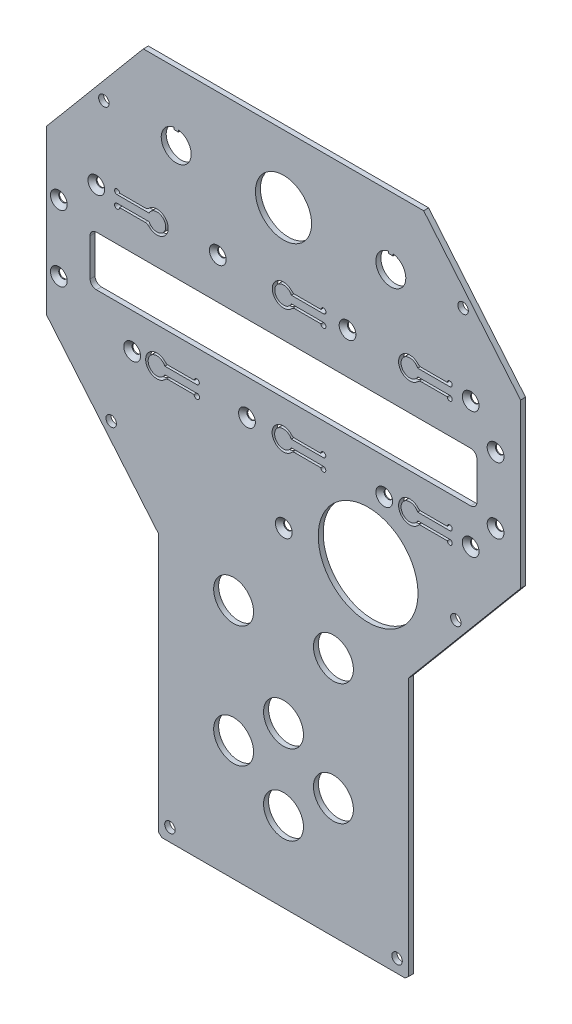
SolidWorks part; units mm, degrees
ref_plane "Plano frontal" through (0, 0, 0) normal (0, 0, 1) x (1, 0, 0)
ref_plane "Plano superior" through (0, 0, 0) normal (0, 1, 0) x (1, 0, 0)
ref_plane "Plano direito" through (0, 0, 0) normal (1, 0, 0) x (0, 0, -1)
sketch "Esboço1" plane through (0, 0, 0) normal (0, 0, 1) x (1, 0, 0)
  line L6 (55.321, 133.8096) -> (-57.007, 133.8096)
  line L7 (-57.007, 133.8096) -> (-95.843, 87.5267)
  line L8 (-95.843, 87.5267) -> (-95.843, 22.1402)
  line L9 (-95.843, 22.1402) -> (-50.843, -31.4887)
  line L10 (-50.843, -31.4887) -> (-50.843, -135.0827)
  line L11 (-50.843, -135.0827) -> (-49.5229, -136.1904)
  line L12 (-49.5229, -136.1904) -> (47.8369, -136.1904)
  line L13 (49.157, -135.0827) -> (47.8369, -136.1904)
  line L14 (49.157, -31.4887) -> (49.157, -135.0827)
  line L15 (94.157, 22.1402) -> (49.157, -31.4887)
  line L16 (94.157, 87.5267) -> (94.157, 22.1402)
  line L17 (55.321, 133.8096) -> (94.157, 87.5267)
  point P1 (0, 0)
  point P2 (0, 0)
  point P16 (-0.843, -136.1904)
  point P17 (-0.843, 133.8096)
  dimension "D2" = 140
extrude "Ressalto-extrusão1" add sketch "Esboço1" along normal blind 2
sketch "Esboço2" plane through (0, 0, 2) normal (0, 0, 1) x (1, 0, 0)
  line L0 (-0.843, -146.6722) -> (-0.843, 180.0647) construction
  line L1 (-95.843, 87.5267) -> (-95.843, 22.1402) construction
  line L2 (55.321, 133.8096) -> (-57.007, 133.8096) construction
  line L3 (-95.843, 22.1402) -> (-50.843, -31.4887) construction
  line L6 (49.157, -135.0827) -> (49.157, -31.4887) construction
  line L7 (-49.5229, -136.1904) -> (47.8369, -136.1904) construction
  line L9 (-50.843, -31.4887) -> (-50.843, -135.0827) construction
  circle A0 centre (-72.8144, 107.9499) radius 2.1
  circle A1 centre (-46.343, -130.9644) radius 2.1
  circle A2 centre (44.657, -130.9644) radius 2.1
  circle A3 centre (71.1284, 107.9499) radius 2.1
  circle A4 centre (-69.8958, -1.7817) radius 2.1
  circle A5 centre (68.2098, -1.7817) radius 2.1
  dimension "D1" = 23.0286
  dimension "D2" = 4.5
  dimension "D3" = 4.5
  dimension "D7" = 25.8597
  dimension "D4" = 5.226
  dimension "D11" = 4.5
extrude "Corte-extrusão1" cut sketch "Esboço2" against normal up to next
sketch "Esboço3" plane through (0, 0, 2) normal (0, 0, 1) x (1, 0, 0)
  line L0 (-95.843, 87.5267) -> (-95.843, 22.1402) construction
  line L1 (-49.5229, -136.1904) -> (47.8369, -136.1904) construction
  line L2 (-75.843, 40.8096) -> (74.157, 40.8096)
  line L3 (-78.343, 43.3096) -> (-78.343, 58.3096)
  line L4 (-75.843, 60.8096) -> (74.157, 60.8096)
  line L5 (76.657, 43.3096) -> (76.657, 58.3096)
  line L6 (-78.343, 40.8096) -> (76.657, 60.8096) construction
  line L7 (-78.343, 60.8096) -> (76.657, 40.8096) construction
  arc A0 (74.157, 60.8096) -> (76.657, 58.3096) centre (74.157, 58.3096) cw
  arc A1 (74.157, 40.8096) -> (76.657, 43.3096) centre (74.157, 43.3096) ccw
  arc A2 (-75.843, 40.8096) -> (-78.343, 43.3096) centre (-75.843, 43.3096) cw
  arc A3 (-78.343, 58.3096) -> (-75.843, 60.8096) centre (-75.843, 58.3096) cw
  dimension "D1" = 2.5
  dimension "D2" = 155
  dimension "D3" = 20
  dimension "D4" = 17.5
  dimension "D5" = 177
extrude "Corte-extrusão2" cut sketch "Esboço3" against normal up to next
sketch "Esboço4" plane through (0, 0, 2) normal (0, 0, 1) x (1, 0, 0)
  line L2 (-49.5229, -136.1904) -> (47.8369, -136.1904) construction
  line L3 (94.157, 22.1402) -> (94.157, 87.5267) construction
  circle A0 centre (33.0563, -0.1904) radius 20
  dimension "D1" = 136
  dimension "D2" = 61.1007
extrude "Corte-extrusão3" cut sketch "Esboço4" against normal up to next
sketch "Esboço5" plane through (0, 0, 2) normal (0, 0, 1) x (1, 0, 0)
  line L1 (-50.843, -31.4887) -> (-50.843, -135.0827) construction
  line L2 (55.321, 133.8096) -> (-57.007, 133.8096) construction
  line L3 (-44.743, 112.7417) -> (-44.743, 111.9417)
  line L4 (-44.743, 111.9417) -> (-42.943, 111.9417)
  line L5 (-42.943, 111.9417) -> (-42.943, 112.7417)
  line L6 (41.257, 112.7417) -> (41.257, 111.9417)
  line L7 (41.257, 111.9417) -> (43.057, 111.9417)
  line L8 (43.057, 111.9417) -> (43.057, 112.7417)
  line L9 (-20.843, -39.5203) -> (19.157, -39.5203) construction
  line L11 (-50.843, -56.8553) -> (49.157, -56.8553) construction
  line L12 (49.157, -135.0827) -> (49.157, -31.4887) construction
  circle A0 centre (-20.843, -88.1059) radius 8
  circle A1 centre (19.157, -88.1059) radius 8
  circle A2 centre (-0.843, -104.1412) radius 8
  circle A3 centre (-0.843, -72.1234) radius 8
  circle A4 centre (-20.843, -39.5203) radius 8
  circle A5 centre (19.157, -39.5203) radius 8
  circle A6 centre (-0.843, 106.8096) radius 11.25
  arc A7 (-44.743, 112.7417) -> (-42.943, 112.7417) centre (-43.843, 106.8096) ccw
  arc A8 (41.257, 112.7417) -> (43.057, 112.7417) centre (42.157, 106.8096) ccw
  point P1 (-0.843, -39.5203)
  point P3 (-20.843, -39.5203)
  point P10 (-0.843, -56.8553)
  dimension "D3" = 40
  dimension "D11" = 27
  dimension "D12" = 43
  dimension "D13" = 43
  dimension "D14" = 22.5
  dimension "D15" = 12
  dimension "D16" = 12
  dimension "D18" = 1.8
  dimension "D19" = 0.9
  dimension "D20" = 0.8
  dimension "D21" = 1.8
  dimension "D22" = 0.9
  dimension "D23" = 0.8
extrude "Corte-extrusão4" cut sketch "Esboço5" against normal up to next
sketch "Esboço10" plane through (0, 0, 2) normal (0, 0, 1) x (1, 0, 0)
  line L3 (94.157, 22.1402) -> (94.157, 87.5267) construction
  line L4 (74.157, 60.8096) -> (-75.843, 60.8096) construction
  circle A0 centre (-61.4827, 26.6206) radius 1.75
  circle A1 centre (-15.4827, 26.6206) radius 1.75
  circle A2 centre (39.5173, 26.6206) radius 1.75
  circle A3 centre (84.131, 37.971) radius 1.6
  circle A4 centre (84.131, 64.471) radius 1.6
  circle A5 centre (-90.869, 64.471) radius 1.6
  circle A6 centre (-90.869, 37.971) radius 1.6
  circle A7 centre (-27.183, 77.1996) radius 1.75
  circle A8 centre (24.817, 77.1996) radius 1.75
  circle A9 centre (-0.7327, -4.3294) radius 2
  dimension "D1" = 69.3401
  dimension "D2" = 16.39
  dimension "D3" = 52
  dimension "D4" = 30.95
  dimension "D5" = 14.75
hole_wizard "Escareado para parafuso Allen sextavado escareado de M32" positions "3DSketch3" profile "Esboço11" countersink size "M3" standard "ISO" end condition through all
sketch3d "3DSketch3"
  point P0 (-90.869, 64.471, 2)
  point P3 (-90.869, 37.971, 2)
  point P6 (-61.4827, 26.6206, 2)
  point P9 (-15.4827, 26.6206, 2)
  point P12 (39.5173, 26.6206, 2)
  point P15 (84.131, 37.971, 2)
  point P18 (84.131, 64.471, 2)
  point P21 (24.817, 77.1996, 2)
  point P24 (-27.183, 77.1996, 2)
  point P32 (-0.7327, -4.3294, 2)
sketch "Esboço11" plane through (-90.869, 64.471, 2) normal (1, 0, 0) x (0, -1, 0)
  line L0 (0, 0) -> (0, 2)
  line L1 (0, 2) -> (1.7, 2)
  line L2 (1.7, 2) -> (1.7, 1.66)
  line L3 (1.7, 1.66) -> (3.36, 0)
  line L5 (3.36, 0) -> (0, 0)
  line L6 (-1.7, 1.66) -> (-3.36, 0) construction
  line L11 (0, -6.35) -> (0, 107.95) construction
  dimension "Thru Hole Dia." = 3.4
  dimension "Thru Hole Depth" = 2
  dimension "Near C'Sink Dia." = 6.72
  dimension "Near C'Sink Angle" = 90
sketch "Esboço12" plane through (0, 0, 2) normal (0, 0, 1) x (1, 0, 0)
  line L0 (-75.843, 40.8096) -> (74.157, 40.8096) construction
  line L1 (74.157, 60.8096) -> (-75.843, 60.8096) construction
  line L2 (94.157, 22.1402) -> (94.157, 87.5267) construction
  line L3 (52.9293, 28.0196) -> (65.767, 28.0196)
  line L5 (64.767, 29.0196) -> (53.5087, 29.0196)
  line L6 (52.9293, 25.0196) -> (65.767, 25.0196)
  line L7 (2.2593, 28.0196) -> (15.097, 28.0196)
  line L8 (64.767, 24.0196) -> (53.5087, 24.0196)
  line L9 (14.097, 24.0196) -> (2.8387, 24.0196)
  line L10 (14.097, 29.0196) -> (2.8387, 29.0196)
  line L11 (2.2593, 25.0196) -> (15.097, 25.0196)
  line L12 (-48.4107, 28.0196) -> (-35.573, 28.0196)
  line L13 (-36.6534, 24.0196) -> (-47.8313, 24.0196)
  line L14 (-36.573, 29.0196) -> (-47.8313, 29.0196)
  line L15 (-48.4107, 25.0196) -> (-35.9821, 25.0196)
  line L25 (2.3293, 77.9796) -> (15.167, 77.9796)
  line L26 (52.9293, 77.9796) -> (65.767, 77.9796)
  line L27 (14.167, 78.9796) -> (2.9087, 78.9796)
  line L28 (2.3293, 74.9796) -> (15.167, 74.9796)
  line L29 (-54.6953, 77.9796) -> (-67.533, 77.9796)
  line L30 (14.167, 73.9796) -> (2.9087, 73.9796)
  line L31 (64.767, 78.9796) -> (53.5087, 78.9796)
  line L32 (52.9293, 74.9796) -> (65.767, 74.9796)
  line L34 (64.767, 73.9796) -> (53.5087, 73.9796)
  line L35 (-66.533, 78.9796) -> (-55.2746, 78.9796)
  line L36 (-54.6953, 74.9796) -> (-67.533, 74.9796)
  line L38 (-66.533, 73.9796) -> (-55.2746, 73.9796)
  arc A0 (53.5087, 29.0196) -> (53.5087, 24.0196) centre (49.767, 26.5196) ccw
  arc A2 (15.097, 25.0196) -> (14.097, 24.0196) centre (15.097, 24.0196) cw
  arc A3 (-47.8313, 29.0196) -> (-47.8313, 24.0196) centre (-51.573, 26.5196) ccw
  arc A4 (-55.2746, 73.9796) -> (-55.2746, 78.9796) centre (-51.533, 76.4796) ccw
  arc A5 (2.9087, 78.9796) -> (2.9087, 73.9796) centre (-0.833, 76.4796) ccw
  arc A6 (53.5087, 78.9796) -> (53.5087, 73.9796) centre (49.767, 76.4796) ccw
  arc A7 (52.9293, 28.0196) -> (52.9293, 25.0196) centre (49.767, 26.5196) ccw
  arc A8 (65.767, 28.0196) -> (64.767, 29.0196) centre (65.767, 29.0196) ccw
  arc A9 (64.767, 24.0196) -> (65.767, 25.0196) centre (65.767, 24.0196) ccw
  arc A10 (15.097, 28.0196) -> (14.097, 29.0196) centre (15.097, 29.0196) ccw
  arc A11 (2.8387, 29.0196) -> (2.8387, 24.0196) centre (-0.903, 26.5196) ccw
  arc A12 (2.2593, 28.0196) -> (2.2593, 25.0196) centre (-0.903, 26.5196) ccw
  arc A13 (-35.573, 28.0196) -> (-36.573, 29.0196) centre (-35.573, 29.0196) ccw
  arc A14 (-35.9821, 25.0196) -> (-36.6534, 24.0196) centre (-35.573, 24.0196) cw
  arc A17 (-48.4107, 28.0196) -> (-48.4107, 25.0196) centre (-51.573, 26.5196) ccw
  arc A22 (15.167, 77.9796) -> (14.167, 78.9796) centre (15.167, 78.9796) ccw
  arc A23 (52.9293, 77.9796) -> (52.9293, 74.9796) centre (49.767, 76.4796) ccw
  arc A24 (2.3293, 77.9796) -> (2.3293, 74.9796) centre (-0.833, 76.4796) ccw
  arc A25 (14.167, 73.9796) -> (15.167, 74.9796) centre (15.167, 73.9796) ccw
  arc A26 (65.767, 77.9796) -> (64.767, 78.9796) centre (65.767, 78.9796) ccw
  arc A27 (64.767, 73.9796) -> (65.767, 74.9796) centre (65.767, 73.9796) ccw
  arc A28 (-54.6953, 74.9796) -> (-54.6953, 77.9796) centre (-51.533, 76.4796) ccw
  arc A29 (-66.533, 78.9796) -> (-67.533, 77.9796) centre (-67.533, 78.9796) ccw
  arc A30 (-67.533, 74.9796) -> (-66.533, 73.9796) centre (-67.533, 73.9796) ccw
  dimension "D2" = 14.29
  dimension "D5" = 15.67
  dimension "D6" = 44.39
  dimension "D7" = 50.6
  dimension "D8" = 50.7
  dimension "D9" = 1
  dimension "D13" = 16
  dimension "D14" = 4.5
  dimension "D15" = 3.5
  dimension "D16" = 3.5
  dimension "D17" = 4.5
  dimension "D10" = 1
  dimension "D18" = 16
  dimension "D22" = 3.5
  dimension "D19" = 44.39
  dimension "D33" = 4.5
  dimension "D38" = 4.5
  dimension "D42" = 1
  dimension "D39" = 3.5
  dimension "D44" = 16
  dimension "D46" = 4.5
  dimension "D47" = 3.5
  dimension "D45" = 16
  dimension "D50" = 4.5
  dimension "D51" = 3.5
  dimension "D52" = 16
  dimension "D21" = 50.67
  dimension "D11" = 3
  dimension "D12" = 1.5
  dimension "D20" = 50.67
  dimension "D23" = 16
  dimension "D40" = 3
  dimension "D41" = 1.5
  dimension "D43" = 1
extrude "Corte-extrusão5" cut sketch "Esboço12" against normal blind 10
fillet "Filete1" radius 2 11 edges at (-47.8313, 24.0196, 1) (2.8387, 24.0196, 1) (53.5087, 73.9796, 1) (-47.8313, 29.0196, 1) (2.8387, 29.0196, 1) (53.5087, 29.0196, 1) (53.5087, 78.9796, 1) (2.9087, 73.9796, 1) (2.9087, 78.9796, 1) (-55.2746, 73.9796, 1) (-55.2746, 78.9796, 1)
sketch "Esboço13" plane through (0, 0, 2) normal (0, 0, 1) x (1, 0, 0)
  line L0 (74.157, 60.8096) -> (-75.843, 60.8096) construction
  line L1 (-95.843, 87.5267) -> (-95.843, 22.1402) construction
  line L2 (94.157, 22.1402) -> (94.157, 87.5267) construction
  circle A0 centre (-75.843, 77.1996) radius 2
  circle A1 centre (74.157, 77.1996) radius 2
  circle A9 centre (74.157, 26.6206) radius 2
  circle A10 centre (39.5173, 26.6206) radius 1.7 construction
  dimension "D1" = 16.39
  dimension "D3" = 20
  dimension "D4" = 0
  dimension "D5" = 20
  dimension "D2" = 20
hole_wizard "Escareado para parafuso Allen sextavado escareado de M33" positions "3DSketch4" profile "Esboço14" countersink size "M3" standard "ISO" end condition through all
sketch3d "3DSketch4"
  point P0 (-75.843, 77.1996, 2)
  point P3 (74.157, 77.1996, 2)
  point P6 (74.157, 26.6206, 2)
sketch "Esboço14" plane through (-75.843, 77.1996, 2) normal (1, 0, 0) x (0, -1, 0)
  line L0 (0, 0) -> (0, 2)
  line L1 (0, 2) -> (1.7, 2)
  line L2 (1.7, 2) -> (1.7, 1.66)
  line L3 (1.7, 1.66) -> (3.36, 0)
  line L5 (3.36, 0) -> (0, 0)
  line L6 (-1.7, 1.66) -> (-3.36, 0) construction
  line L11 (0, -6.35) -> (0, 107.95) construction
  dimension "Thru Hole Dia." = 3.4
  dimension "Thru Hole Depth" = 2
  dimension "Near C'Sink Dia." = 6.72
  dimension "Near C'Sink Angle" = 90
